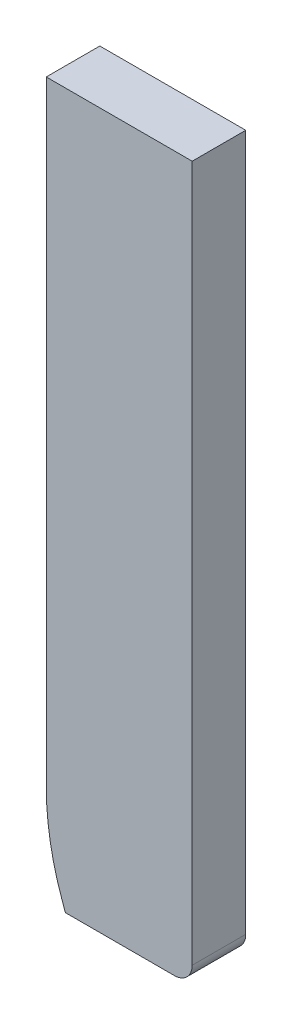
SolidWorks part; units mm, degrees
ref_plane "Alzado" through (0, 0, 0) normal (0, 0, 1) x (1, 0, 0)
ref_plane "Planta" through (0, 0, 0) normal (0, 1, 0) x (1, 0, 0)
ref_plane "Vista lateral" through (0, 0, 0) normal (1, 0, 0) x (0, 0, -1)
sketch "Model" plane through (0, 0, 0) normal (0, 0, 1) x (1, 0, 0)
  line L0 (27.8696, 31.0262) -> (27.8696, 41.2271)
  line L1 (27.8696, 41.2271) -> (27.8696, 50.428)
  line L2 (27.8696, 50.428) -> (27.8696, 65.428)
  line L3 (27.8696, 65.428) -> (36.0424, 65.428)
  line L4 (36.0424, 65.428) -> (36.0424, 64.428)
  line L5 (36.0424, 64.428) -> (36.0424, 45.928)
  line L6 (36.0424, 45.928) -> (36.0424, 26.428)
  line L7 (35.0424, 25.428) -> (28.941, 25.428)
  line L8 (28.941, 25.428) -> (28.7435, 25.9812)
  arc A0 (27.8696, 31.0262) -> (28.7435, 25.9812) centre (42.8696, 31.0262) ccw
  arc A1 (35.0424, 25.428) -> (36.0424, 26.428) centre (35.0424, 26.428) ccw
extrude "Saliente-Extruir1" add sketch "Model" along normal blind 3
